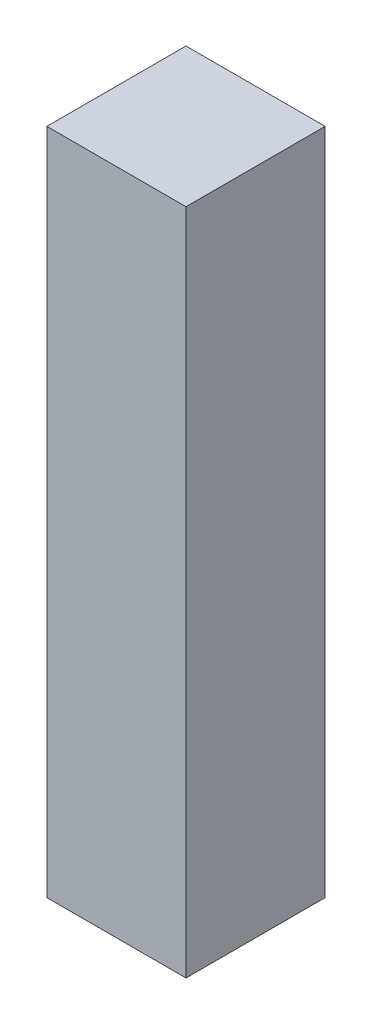
SolidWorks part; units mm, degrees
ref_plane "Front Plane" through (0, 0, 0) normal (0, 0, 1) x (1, 0, 0)
ref_plane "Top Plane" through (0, 0, 0) normal (0, 1, 0) x (1, 0, 0)
ref_plane "Right Plane" through (0, 0, 0) normal (1, 0, 0) x (0, 0, -1)
sketch "Sketch1" plane through (0, 0, 0) normal (0, 0, 1) x (1, 0, 0)
  line L0 (0, 0) -> (-100, 0)
  line L1 (-100, 0) -> (-100, 480)
  line L2 (-100, 480) -> (0, 480)
  line L3 (0, 480) -> (0, 0)
  dimension "D1" = 480
  dimension "D2" = 100
extrude "Boss-Extrude1" add sketch "Sketch1" along normal blind 100 separate body contours L3 L0 L1 L2
